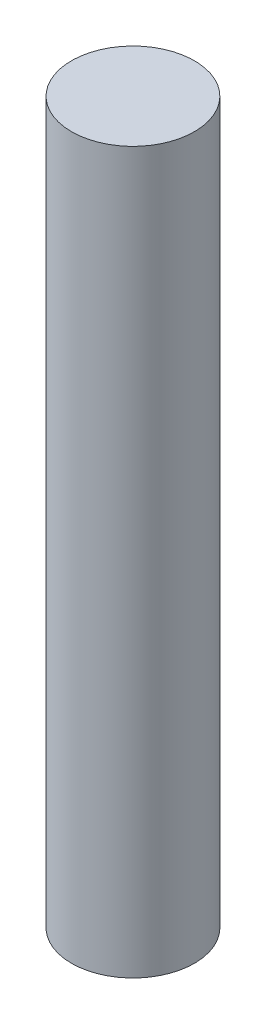
SolidWorks part; units mm, degrees
material "2024 Alloy"
ref_plane "Front Plane" through (0, 0, 0) normal (0, 0, 1) x (1, 0, 0)
ref_plane "Top Plane" through (0, 0, 0) normal (0, 1, 0) x (1, 0, 0)
ref_plane "Right Plane" through (0, 0, 0) normal (1, 0, 0) x (0, 0, -1)
sketch "Sketch1" plane through (0, 0, 0) normal (0, 1, 0) x (1, 0, 0)
  circle A0 centre (0, 0) radius 7.9375
extrude "Boss-Extrude1" add sketch "Sketch1" along normal blind 93
